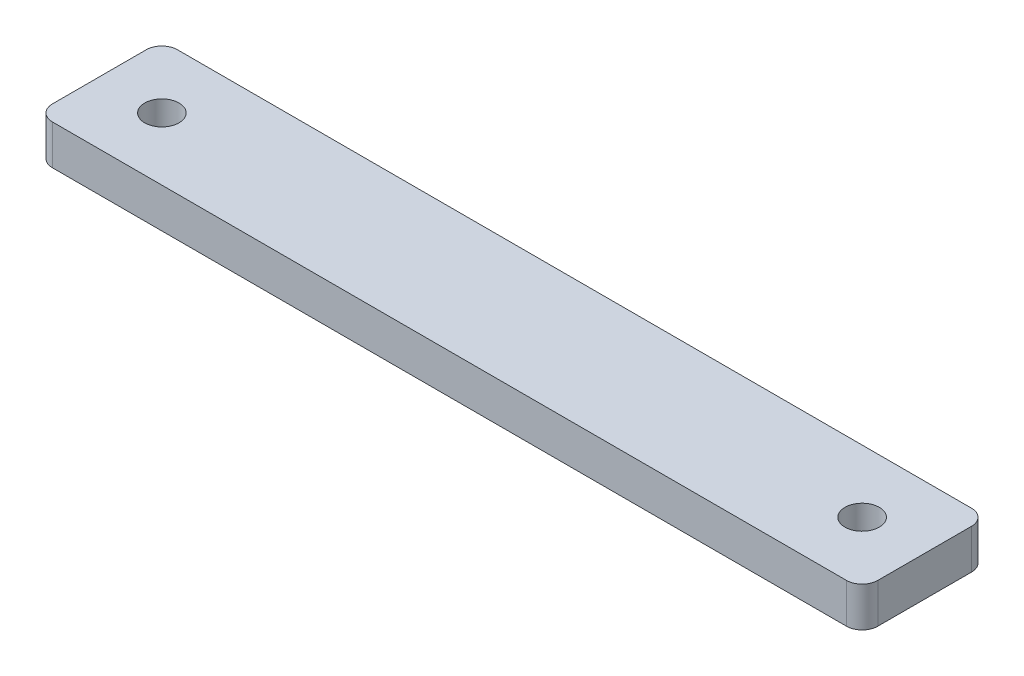
SolidWorks part; units mm, degrees
material "6061-T6 (SS)"
ref_plane "Front Plane" through (0, 0, 0) normal (0, 0, 1) x (1, 0, 0)
ref_plane "Top Plane" through (0, 0, 0) normal (0, 1, 0) x (1, 0, 0)
ref_plane "Right Plane" through (0, 0, 0) normal (1, 0, 0) x (0, 0, -1)
sketch "Sketch1" plane through (0, 0, 0) normal (0, 1, 0) x (1, 0, 0)
  line L1 (66, -10) -> (-66, -10)
  line L2 (66, -10) -> (66, 10)
  line L3 (66, 10) -> (-66, 10)
  line L4 (-66, -10) -> (-66, 10)
  line L5 (66, -10) -> (-66, 10) construction
  line L6 (66, 10) -> (-66, -10) construction
  circle A0 centre (-56, 0) radius 2.75
  circle A1 centre (56, 0) radius 2.75
  point P0 (0, 0)
  dimension "D7" = 5.5
  dimension "D8" = 5.5
  dimension "D1" = 132
  dimension "D2" = 20
  dimension "D3" = 10
  dimension "D4" = 10
  dimension "D5" = 10
  dimension "D6" = 10
extrude "Boss-Extrude1" add sketch "Sketch1" along normal blind 6.35
fillet "Fillet1" radius 2.5 4 edges at (66, 3.175, -10) (66, 3.175, 10) (-66, 3.175, 10) (-66, 3.175, -10)
